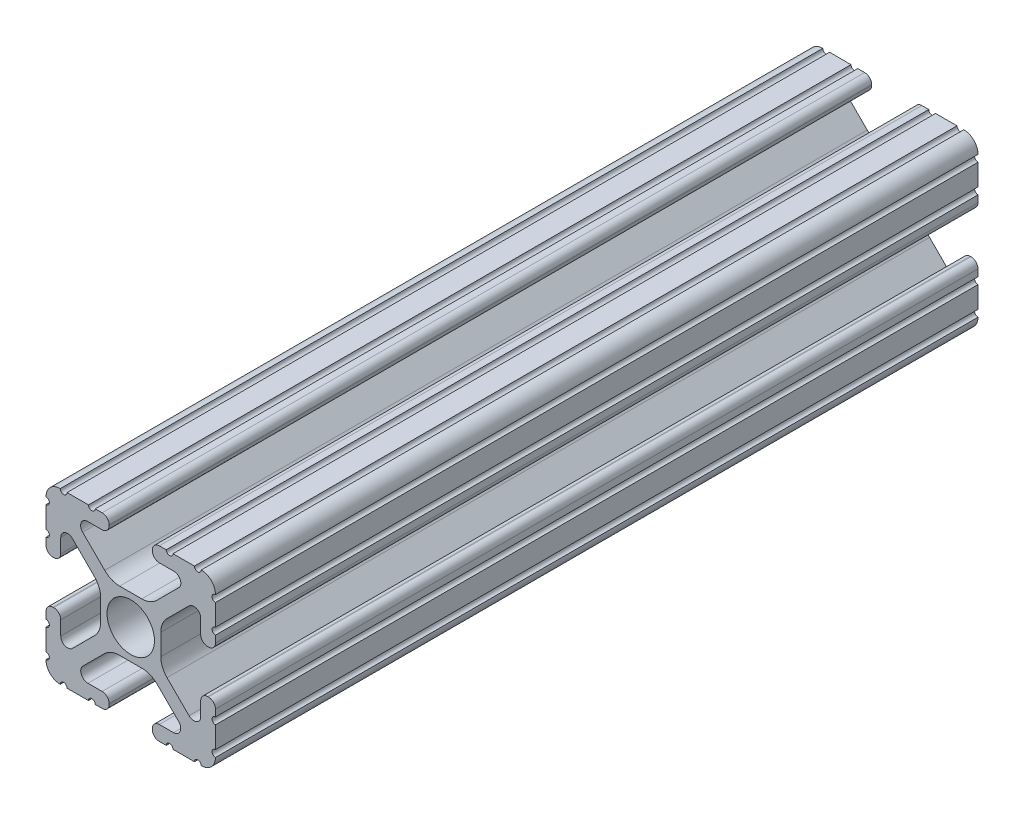
SolidWorks part; units mm, degrees
ref_plane "Front Plane" through (0, 0, 0) normal (0, 0, 1) x (1, 0, 0)
ref_plane "Top Plane" through (0, 0, 0) normal (0, 1, 0) x (1, 0, 0)
ref_plane "Right Plane" through (0, 0, 0) normal (1, 0, 0) x (0, 0, -1)
sketch "Sketch1" plane through (0, 0, 0) normal (0, 0, 1) x (1, 0, 0)
  line L88 (-7.1797, -8.6452) -> (-3.9523, -5.4237)
  line L89 (-1.7093, -4.4958) -> (1.7093, -4.4958)
  line L90 (3.9523, -5.4237) -> (7.1797, -8.6452)
  line L91 (6.4164, -10.4902) -> (4.2875, -10.4902)
  line L92 (3.2385, -11.5392) -> (3.2385, -11.651)
  line L93 (4.2875, -12.7) -> (5.3171, -12.7)
  line L94 (6.3331, -12.7) -> (9.5504, -12.7)
  line L95 (12.7, -9.5504) -> (12.7, -6.3331)
  line L96 (12.7, -5.3171) -> (12.7, -4.2875)
  line L97 (11.651, -3.2385) -> (11.5392, -3.2385)
  line L98 (10.4902, -4.2875) -> (10.4902, -6.4021)
  line L99 (8.7371, -7.1294) -> (5.441, -3.8408)
  line L100 (4.5085, -1.5932) -> (4.5085, 1.5932)
  line L101 (5.441, 3.8408) -> (8.7371, 7.1294)
  line L102 (10.4902, 6.4021) -> (10.4902, 4.2875)
  line L103 (11.5392, 3.2385) -> (11.651, 3.2385)
  line L104 (12.7, 4.2875) -> (12.7, 5.3171)
  line L105 (12.7, 6.3331) -> (12.7, 9.5504)
  line L106 (9.5504, 12.7) -> (6.3331, 12.7)
  line L107 (5.3171, 12.7) -> (4.2875, 12.7)
  line L108 (3.2385, 11.651) -> (3.2385, 11.5392)
  line L109 (4.2875, 10.4902) -> (6.4768, 10.4902)
  line L110 (7.207, 8.7244) -> (3.8983, 5.4232)
  line L111 (1.6558, 4.4958) -> (-1.6558, 4.4958)
  line L112 (-3.8983, 5.4232) -> (-7.207, 8.7244)
  line L113 (-6.4768, 10.4902) -> (-4.2875, 10.4902)
  line L114 (-3.2385, 11.5392) -> (-3.2385, 11.651)
  line L115 (-4.2875, 12.7) -> (-5.3171, 12.7)
  line L116 (-6.3331, 12.7) -> (-9.5504, 12.7)
  line L117 (-12.7, 9.5504) -> (-12.7, 6.3331)
  line L118 (-12.7, 5.3171) -> (-12.7, 4.2875)
  line L119 (-11.651, 3.2385) -> (-11.5392, 3.2385)
  line L120 (-10.4902, 4.2875) -> (-10.4902, 6.4021)
  line L121 (-8.7371, 7.1294) -> (-5.441, 3.8408)
  line L122 (-4.5085, 1.5932) -> (-4.5085, -1.5932)
  line L123 (-5.441, -3.8408) -> (-8.7371, -7.1294)
  line L124 (-10.4902, -6.4021) -> (-10.4902, -4.2875)
  line L125 (-11.5392, -3.2385) -> (-11.651, -3.2385)
  line L126 (-12.7, -4.2875) -> (-12.7, -5.3171)
  line L127 (-12.7, -6.3331) -> (-12.7, -9.5504)
  line L128 (-9.5504, -12.7) -> (-6.3331, -12.7)
  line L129 (-5.3171, -12.7) -> (-4.2875, -12.7)
  line L130 (-3.2385, -11.651) -> (-3.2385, -11.5392)
  line L131 (-4.2875, -10.4902) -> (-6.4164, -10.4902)
  circle A0 centre (0, 0) radius 3.556
  arc A104 (-7.1797, -8.6452) -> (-6.4164, -10.4902) centre (-6.4164, -9.4098) ccw
  arc A105 (-1.7093, -4.4958) -> (-3.9523, -5.4237) centre (-1.7093, -7.6708) ccw
  arc A106 (3.9523, -5.4237) -> (1.7093, -4.4958) centre (1.7093, -7.6708) ccw
  arc A107 (6.4164, -10.4902) -> (7.1797, -8.6452) centre (6.4164, -9.4098) ccw
  arc A108 (4.2875, -10.4902) -> (3.2385, -11.5392) centre (4.2875, -11.5392) ccw
  arc A109 (3.2385, -11.651) -> (4.2875, -12.7) centre (4.2875, -11.651) ccw
  arc A110 (6.3331, -12.7) -> (5.3171, -12.7) centre (5.8251, -12.7) ccw
  arc A111 (10.5664, -12.6998) -> (9.5504, -12.7) centre (10.0584, -12.7) ccw
  arc A112 (10.5664, -12.6998) -> (12.6998, -10.5664) centre (10.5918, -10.5918) ccw
  arc A113 (12.7, -9.5504) -> (12.6998, -10.5664) centre (12.7, -10.0584) ccw
  arc A114 (12.7, -5.3171) -> (12.7, -6.3331) centre (12.7, -5.8251) ccw
  arc A115 (12.7, -4.2875) -> (11.651, -3.2385) centre (11.651, -4.2875) ccw
  arc A116 (11.5392, -3.2385) -> (10.4902, -4.2875) centre (11.5392, -4.2875) ccw
  arc A117 (8.7371, -7.1294) -> (10.4902, -6.4021) centre (9.4628, -6.4021) ccw
  arc A118 (4.5085, -1.5932) -> (5.441, -3.8408) centre (7.6835, -1.5932) ccw
  arc A119 (5.441, 3.8408) -> (4.5085, 1.5932) centre (7.6835, 1.5932) ccw
  arc A120 (10.4902, 6.4021) -> (8.7371, 7.1294) centre (9.4628, 6.4021) ccw
  arc A121 (10.4902, 4.2875) -> (11.5392, 3.2385) centre (11.5392, 4.2875) ccw
  arc A122 (11.651, 3.2385) -> (12.7, 4.2875) centre (11.651, 4.2875) ccw
  arc A123 (12.7, 6.3331) -> (12.7, 5.3171) centre (12.7, 5.8251) ccw
  arc A124 (12.6998, 10.5664) -> (12.7, 9.5504) centre (12.7, 10.0584) ccw
  arc A125 (12.6998, 10.5664) -> (10.5664, 12.6998) centre (10.5918, 10.5918) ccw
  arc A126 (9.5504, 12.7) -> (10.5664, 12.6998) centre (10.0584, 12.7) ccw
  arc A127 (5.3171, 12.7) -> (6.3331, 12.7) centre (5.8251, 12.7) ccw
  arc A128 (4.2875, 12.7) -> (3.2385, 11.651) centre (4.2875, 11.651) ccw
  arc A129 (3.2385, 11.5392) -> (4.2875, 10.4902) centre (4.2875, 11.5392) ccw
  arc A130 (7.207, 8.7244) -> (6.4768, 10.4902) centre (6.4768, 9.4563) ccw
  arc A131 (1.6558, 4.4958) -> (3.8983, 5.4232) centre (1.6558, 7.6708) ccw
  arc A132 (-3.8983, 5.4232) -> (-1.6558, 4.4958) centre (-1.6558, 7.6708) ccw
  arc A133 (-6.4768, 10.4902) -> (-7.207, 8.7244) centre (-6.4768, 9.4563) ccw
  arc A134 (-4.2875, 10.4902) -> (-3.2385, 11.5392) centre (-4.2875, 11.5392) ccw
  arc A135 (-3.2385, 11.651) -> (-4.2875, 12.7) centre (-4.2875, 11.651) ccw
  arc A136 (-6.3331, 12.7) -> (-5.3171, 12.7) centre (-5.8251, 12.7) ccw
  arc A137 (-10.5664, 12.6998) -> (-9.5504, 12.7) centre (-10.0584, 12.7) ccw
  arc A138 (-10.5664, 12.6998) -> (-12.6998, 10.5664) centre (-10.5918, 10.5918) ccw
  arc A139 (-12.7, 9.5504) -> (-12.6998, 10.5664) centre (-12.7, 10.0584) ccw
  arc A140 (-12.7, 5.3171) -> (-12.7, 6.3331) centre (-12.7, 5.8251) ccw
  arc A141 (-12.7, 4.2875) -> (-11.651, 3.2385) centre (-11.651, 4.2875) ccw
  arc A142 (-11.5392, 3.2385) -> (-10.4902, 4.2875) centre (-11.5392, 4.2875) ccw
  arc A143 (-8.7371, 7.1294) -> (-10.4902, 6.4021) centre (-9.4628, 6.4021) ccw
  arc A144 (-4.5085, 1.5932) -> (-5.441, 3.8408) centre (-7.6835, 1.5932) ccw
  arc A145 (-5.441, -3.8408) -> (-4.5085, -1.5932) centre (-7.6835, -1.5932) ccw
  arc A146 (-10.4902, -6.4021) -> (-8.7371, -7.1294) centre (-9.4628, -6.4021) ccw
  arc A147 (-10.4902, -4.2875) -> (-11.5392, -3.2385) centre (-11.5392, -4.2875) ccw
  arc A148 (-11.651, -3.2385) -> (-12.7, -4.2875) centre (-11.651, -4.2875) ccw
  arc A149 (-12.7, -6.3331) -> (-12.7, -5.3171) centre (-12.7, -5.8251) ccw
  arc A150 (-12.6998, -10.5664) -> (-12.7, -9.5504) centre (-12.7, -10.0584) ccw
  arc A151 (-12.6998, -10.5664) -> (-10.5664, -12.6998) centre (-10.5918, -10.5918) ccw
  arc A152 (-9.5504, -12.7) -> (-10.5664, -12.6998) centre (-10.0584, -12.7) ccw
  arc A153 (-5.3171, -12.7) -> (-6.3331, -12.7) centre (-5.8251, -12.7) ccw
  arc A154 (-4.2875, -12.7) -> (-3.2385, -11.651) centre (-4.2875, -11.651) ccw
  arc A155 (-3.2385, -11.5392) -> (-4.2875, -10.4902) centre (-4.2875, -11.5392) ccw
  dimension "D1" = 7.112
extrude "Boss-Extrude1" add sketch "Sketch1" along normal mid plane 114.3
